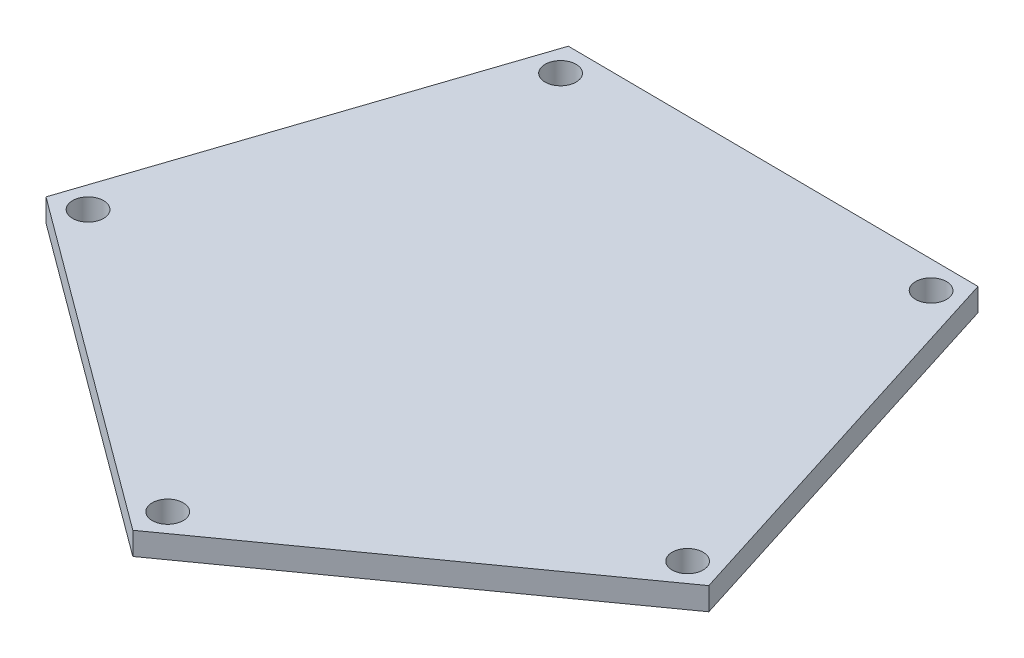
SolidWorks part; units mm, degrees
ref_plane "Front Plane" through (0, 0, 0) normal (0, 0, 1) x (1, 0, 0)
ref_plane "Top Plane" through (0, 0, 0) normal (0, 1, 0) x (1, 0, 0)
ref_plane "Right Plane" through (0, 0, 0) normal (1, 0, 0) x (0, 0, -1)
sketch "Sketch1" plane through (0, 0, 0) normal (0, 1, 0) x (1, 0, 0)
  line L0 (-98.9156, 138.4195) -> (-80.0244, 111.9838) construction
  line L1 (161.3854, -53.8426) -> (101.0782, 136.8484)
  line L2 (101.0782, 136.8484) -> (-98.9156, 138.4195)
  line L3 (-98.9156, 138.4195) -> (-162.2114, -51.3004)
  line L4 (-162.2114, -51.3004) -> (-1.3365, -170.1249)
  line L5 (-1.3365, -170.1249) -> (161.3854, -53.8426)
  line L6 (101.0782, 136.8484) -> (81.774, 110.7126) construction
  line L7 (-1.3365, -170.1249) -> (0, -137.6382) construction
  line L8 (161.3854, -53.8426) -> (130.5635, -43.5596) construction
  line L9 (-31.6377, -10.0056) -> (-194.5072, -61.5141) construction
  line L10 (-162.2114, -51.3004) -> (-131.2239, -41.5277) construction
  line L13 (101.0782, 136.8484) -> (-61.7913, 85.3398) construction
  line L14 (-61.7913, 85.3398) -> (-1.4841, -105.3511) construction
  line L15 (-1.4841, -105.3511) -> (161.3854, -53.8426) construction
  circle A0 centre (0, 0) radius 137.6382 construction
  circle A1 centre (-89.47, 125.2016) radius 7.5
  circle A3 centre (-146.7177, -46.4141) radius 7.5
  circle A4 centre (-0.6683, -153.8816) radius 7.5
  circle A5 centre (145.9745, -48.7011) radius 7.5
  circle A6 centre (91.4261, 123.7805) radius 7.5
  dimension "D1" = 200
extrude "Boss-Extrude4" add sketch "Sketch1" along normal blind 11
sketch "Sketch2" plane through (0, 0, 0) normal (0, -1, 0) x (-1, 0, 0)
  line L1 (-189.7199, -63.2958) -> (-40.0442, -195.9501)
  line L2 (-40.0442, -195.9501) -> (149.6757, -132.6544)
  line L3 (149.6757, -132.6544) -> (189.7199, 63.2958)
  line L4 (189.7199, 63.2958) -> (40.0442, 195.9501)
  line L5 (40.0442, 195.9501) -> (-149.6757, 132.6544)
  line L6 (-149.6757, 132.6544) -> (-189.7199, -63.2958)
  circle A0 centre (0, 0) radius 173.2051 construction
  dimension "D1" = 200
